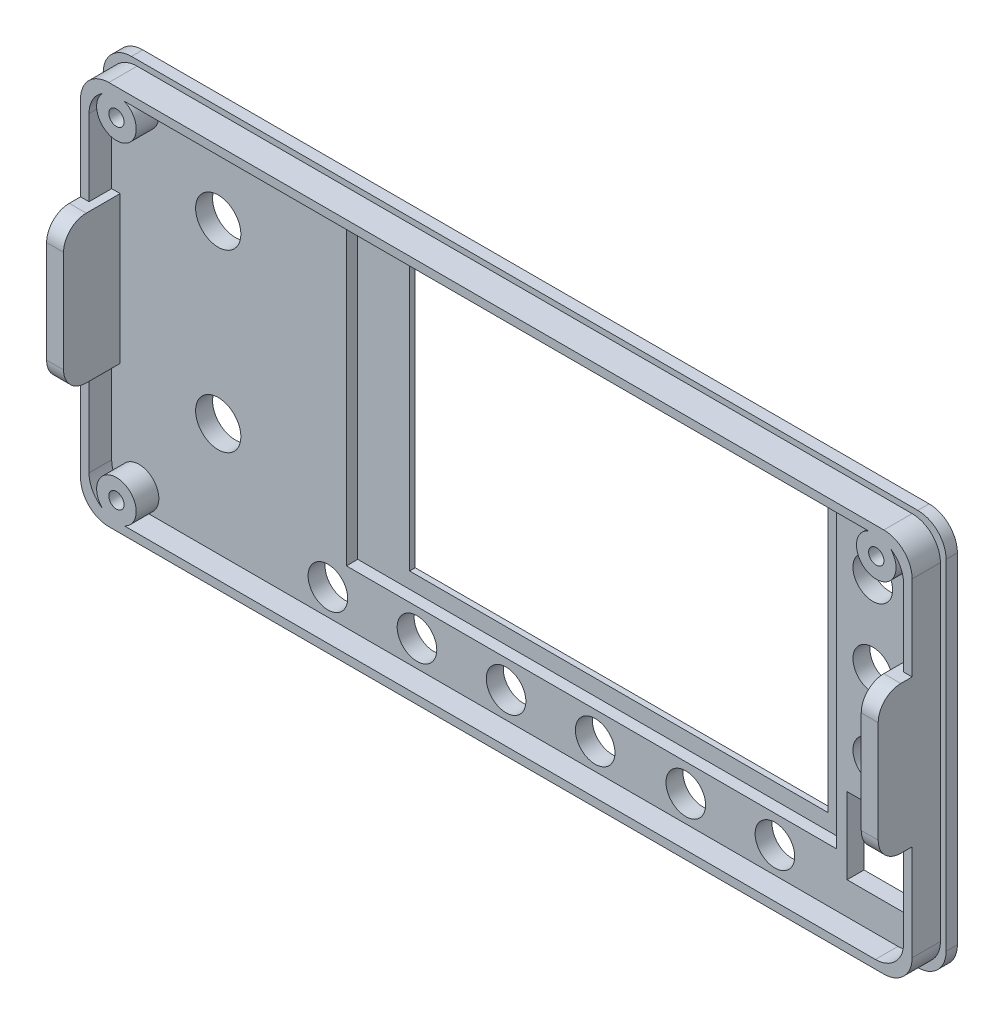
SolidWorks part; units mm, degrees
material "ПК/АБС"
ref_plane "Спереди" through (0, 0, 0) normal (0, 0, 1) x (1, 0, 0)
ref_plane "Сверху" through (0, 0, 0) normal (0, 1, 0) x (1, 0, 0)
ref_plane "Справа" through (0, 0, 0) normal (1, 0, 0) x (0, 0, -1)
sketch "Эскиз1" plane through (0, 0, 0) normal (0, 0, 1) x (1, 0, 0)
  line L1 (74.5, -35) -> (-74.5, -35)
  line L2 (74.5, -35) -> (74.5, 35)
  line L3 (74.5, 35) -> (-74.5, 35)
  line L4 (-74.5, -35) -> (-74.5, 35)
  line L5 (74.5, -35) -> (-74.5, 35) construction
  line L6 (74.5, 35) -> (-74.5, -35) construction
  point P0 (0, 0)
  dimension "D1" = 149
  dimension "D2" = 70
extrude "Бобышка-Вытянуть1" add sketch "Эскиз1" along normal blind 1
sketch "Эскиз2" plane through (0, 0, 1) normal (0, 0, 1) x (1, 0, 0)
  line L1 (73.5, -34) -> (-73.5, -34)
  line L2 (73.5, -34) -> (73.5, 34)
  line L3 (73.5, 34) -> (-73.5, 34)
  line L4 (-73.5, -34) -> (-73.5, 34)
  line L5 (73.5, -34) -> (-73.5, 34) construction
  line L6 (73.5, 34) -> (-73.5, -34) construction
  point P0 (0, 0)
  dimension "D1" = 147
  dimension "D2" = 68
extrude "Бобышка-Вытянуть2" add sketch "Эскиз2" along normal blind 2
fillet "Скругление1" radius 5 8 edges at (74.5, -35, 0.5) (73.5, -34, 2) (74.5, 35, 0.5) (73.5, 34, 2) (-74.5, -35, 0.5) (-73.5, -34, 2) (-74.5, 35, 0.5) (-73.5, 34, 2)
sketch "Эскиз3" plane through (0, 0, 3) normal (0, 0, 1) x (1, 0, 0)
  line L6 (-73.5, 29) -> (-73.5, -29) construction
  line L7 (-73.5, 14) -> (-70.5, 14)
  line L8 (-73.5, 14) -> (-73.5, -12)
  line L9 (-73.5, -12) -> (-70.5, -12)
  line L10 (-70.5, 14) -> (-70.5, -12)
  line L11 (73.5, 14) -> (70.5, 14)
  line L12 (73.5, 14) -> (73.5, -12)
  line L13 (73.5, -12) -> (70.5, -12)
  line L14 (70.5, 14) -> (70.5, -12)
  dimension "D1" = 3
extrude "Бобышка-Вытянуть3" add sketch "Эскиз3" along normal blind 10
fillet "Скругление2" radius 4 4 edges at (72, -12, 13) (72, 14, 13) (-72, -12, 13) (-72, 14, 13)
sketch "Эскиз6" plane through (0, 0, 3) normal (0, 0, 1) x (1, 0, 0)
  circle A0 centre (-67.16, 29.285) radius 3.5
  circle A1 centre (67.16, 29.285) radius 3.5
  circle A3 centre (-67.16, -29.285) radius 3.5
  point P0 (0, 0)
  dimension "D3" = 7
  dimension "D4" = 7
  dimension "D5" = 7
  dimension "D1" = 134.32
extrude "Бобышка-Вытянуть4" add sketch "Эскиз6" along normal blind 4
sketch "Эскиз7" plane through (0, 0, 3) normal (0, 0, 1) x (1, 0, 0)
  line L0 (68.5, 34) -> (-68.5, 34) construction
  line L1 (-30.5, 32.5) -> (56.16, 32.5)
  line L2 (-30.5, 32.5) -> (-30.5, -23)
  line L3 (-30.5, -23) -> (56.16, -23)
  line L4 (56.16, 32.5) -> (56.16, -23)
  line L5 (-73.5, 29) -> (-73.5, 14) construction
  line L6 (-68.5, -34) -> (68.5, -34) construction
  circle A0 centre (67.16, 29.285) radius 3.5 construction
  dimension "D1" = 43
  dimension "D2" = 11
  dimension "D3" = 11
  dimension "D4" = 1.5
extrude "Вырез-Вытянуть3" cut sketch "Эскиз7" against normal blind 2
sketch "Эскиз8" plane through (0, 0, 1) normal (0, 0, 1) x (1, 0, 0)
  line L2 (56.16, -23) -> (56.16, 32.5) construction
  line L5 (-30.5, -23) -> (56.16, -23) construction
  line L7 (-21.34, 28.8) -> (52.66, 28.8)
  line L8 (-21.34, 28.8) -> (-21.34, -20.2)
  line L9 (-21.34, -20.2) -> (52.66, -20.2)
  line L10 (52.66, 28.8) -> (52.66, -20.2)
  dimension "D1" = 74
  dimension "D2" = 49
  dimension "D3" = 3.5
  dimension "D4" = 2.8
extrude "Вырез-Вытянуть4" cut sketch "Эскиз8" against normal through all
sketch "Эскиз9" plane through (0, 0, 3) normal (0, 0, 1) x (1, 0, 0)
  circle A1 centre (62.54, -6.405) radius 3.5
  circle A2 centre (62.54, 21.595) radius 3.5
  circle A3 centre (62.54, 7.595) radius 3.5
  circle A4 centre (67.16, 29.285) radius 3.5 construction
  circle A5 centre (67.16, 29.285) radius 3.5 construction
  dimension "D6" = 7
  dimension "D1" = 7
  dimension "D2" = 7
  dimension "D3" = 4.62
  dimension "D4" = 7.69
  dimension "D5" = 14
  dimension "D7" = 14
sketch "Эскиз11" plane through (0, 0, 3) normal (0, 0, 1) x (1, 0, 0)
  circle A0 centre (-53.163, 18.448) radius 4
  circle A1 centre (-67.16, 29.285) radius 3.5 construction
  circle A2 centre (-53.163, -12.552) radius 4
  dimension "D1" = 13.997
  dimension "D2" = 10.837
  dimension "D3" = 8
  dimension "D4" = 8
  dimension "D5" = 31
extrude "Вырез-Вытянуть7" cut sketch "Эскиз11" against normal through all
sketch "Эскиз12" plane through (0, 0, 7) normal (0, 0, 1) x (1, 0, 0)
  circle A0 centre (-67.16, 29.285) radius 1.35
  dimension "D1" = 2.7
extrude "Вырез-Вытянуть8" cut sketch "Эскиз12" against normal blind 4
sketch "Эскиз13" plane through (0, 0, 7) normal (0, 0, 1) x (1, 0, 0)
  circle A0 centre (67.16, 29.285) radius 1.35
  dimension "D1" = 2.7
extrude "Вырез-Вытянуть9" cut sketch "Эскиз13" against normal blind 4
sketch "Эскиз14" plane through (0, 0, 7) normal (0, 0, 1) x (1, 0, 0)
  circle A0 centre (-67.16, -29.285) radius 1.35
  dimension "D1" = 2.7
extrude "Вырез-Вытянуть10" cut sketch "Эскиз14" against normal blind 4
sketch "Эскиз15" plane through (0, 0, 3) normal (0, 0, 1) x (1, 0, 0)
  line L1 (58, -13.3) -> (72, -13.3)
  line L2 (58, -13.3) -> (58, -26.8)
  line L3 (58, -26.8) -> (72, -26.8)
  line L4 (72, -13.3) -> (72, -26.8)
  line L9 (73.5, -29) -> (73.5, -12) construction
  line L10 (-68.5, -34) -> (68.5, -34) construction
  dimension "D1" = 14
  dimension "D2" = 1.5
  dimension "D3" = 13.5
  dimension "D4" = 7.2
extrude "Вырез-Вытянуть11" cut sketch "Эскиз15" against normal through all
extrude "Вырез-Вытянуть12" cut sketch "Эскиз9" against normal through all
sketch "Эскиз16" plane through (0, 0, 3) normal (0, 0, 1) x (1, 0, 0)
  circle A0 centre (45.24, -27.88) radius 3.5
  circle A1 centre (62.54, -6.405) radius 3.5 construction
  circle A2 centre (29.49, -27.88) radius 3.5
  circle A3 centre (13.47, -27.88) radius 3.5
  circle A4 centre (-2.28, -27.88) radius 3.5
  circle A5 centre (-18.03, -27.88) radius 3.5
  circle A6 centre (-33.78, -27.88) radius 3.5
  dimension "D1" = 17.3
  dimension "D2" = 21.475
  dimension "D3" = 7
  dimension "D4" = 7
  dimension "D5" = 7
  dimension "D6" = 7
  dimension "D7" = 15.75
  dimension "D9" = 15.75
  dimension "D10" = 7
  dimension "D11" = 7
  dimension "D12" = 15.75
  dimension "D13" = 15.75
extrude "Вырез-Вытянуть13" cut sketch "Эскиз16" against normal through all
sketch "Эскиз17" plane through (0, 0, 3) normal (0, 0, 1) x (1, 0, 0)
  line L0 (68.5, 34) -> (-68.5, 34) construction
  line L1 (67, -32.5) -> (-67, -32.5)
  line L2 (72, -27.5) -> (72, 27.5)
  line L3 (67, 32.5) -> (-67, 32.5)
  line L4 (-72, -27.5) -> (-72, 27.5)
  line L5 (72, -32.5) -> (-72, 32.5) construction
  line L6 (72, 32.5) -> (-72, -32.5) construction
  line L7 (-73.5, 29) -> (-73.5, -29) construction
  line L8 (-73.5, 29) -> (-73.5, 14) construction
  line L9 (68.5, -34) -> (-68.5, -34)
  line L10 (73.5, -29) -> (73.5, 29)
  line L11 (68.5, 34) -> (-68.5, 34)
  line L12 (-73.5, -29) -> (-73.5, 29)
  line L13 (73.5, -34) -> (-73.5, 34) construction
  line L14 (73.5, 34) -> (-73.5, -34) construction
  arc A0 (72, 27.5) -> (67, 32.5) centre (67, 27.5) ccw
  arc A1 (72, -27.5) -> (67, -32.5) centre (67, -27.5) cw
  arc A2 (-72, -27.5) -> (-67, -32.5) centre (-67, -27.5) ccw
  arc A3 (-72, 27.5) -> (-67, 32.5) centre (-67, 27.5) cw
  arc A4 (73.5, 29) -> (68.5, 34) centre (68.5, 29) ccw
  arc A5 (68.5, -34) -> (73.5, -29) centre (68.5, -29) ccw
  arc A6 (-73.5, -29) -> (-68.5, -34) centre (-68.5, -29) ccw
  arc A7 (-73.5, 29) -> (-68.5, 34) centre (-68.5, 29) cw
  point P0 (0, 0)
  point P22 (0, 0)
  dimension "D3" = 5
  dimension "D5" = 5
  dimension "D1" = 1.5
  dimension "D2" = 1.5
  dimension "D4" = 0
extrude "Бобышка-Вытянуть5" add sketch "Эскиз17" along normal blind 4
sketch "Эскиз18" plane through (0, 0, 1) normal (0, 0, 1) x (1, 0, 0)
  line L1 (69.5, -35) -> (-69.5, -35)
  line L2 (74.5, -30) -> (74.5, 30)
  line L3 (69.5, 35) -> (-69.5, 35)
  line L4 (-74.5, -30) -> (-74.5, 30)
  line L5 (74.5, -35) -> (-74.5, 35) construction
  line L6 (74.5, 35) -> (-74.5, -35) construction
  line L7 (68.5, -34) -> (-68.5, -34)
  line L8 (73.5, -29) -> (73.5, 29)
  line L9 (68.5, 34) -> (-68.5, 34)
  line L10 (-73.5, -29) -> (-73.5, 29)
  line L11 (73.5, -34) -> (-73.5, 34) construction
  line L12 (73.5, 34) -> (-73.5, -34) construction
  arc A0 (74.5, 30) -> (69.5, 35) centre (69.5, 30) ccw
  arc A1 (74.5, -30) -> (69.5, -35) centre (69.5, -30) cw
  arc A2 (-74.5, -30) -> (-69.5, -35) centre (-69.5, -30) ccw
  arc A3 (-74.5, 30) -> (-69.5, 35) centre (-69.5, 30) cw
  arc A4 (-73.5, -29) -> (-68.5, -34) centre (-68.5, -29) ccw
  arc A5 (73.5, -29) -> (68.5, -34) centre (68.5, -29) cw
  arc A6 (73.5, 29) -> (68.5, 34) centre (68.5, 29) ccw
  arc A7 (-73.5, 29) -> (-68.5, 34) centre (-68.5, 29) cw
  point P0 (0, 0)
  point P18 (0, 0)
  dimension "D1" = 5
  dimension "D2" = 5
extrude "Бобышка-Вытянуть6" add sketch "Эскиз18" along normal blind 1
